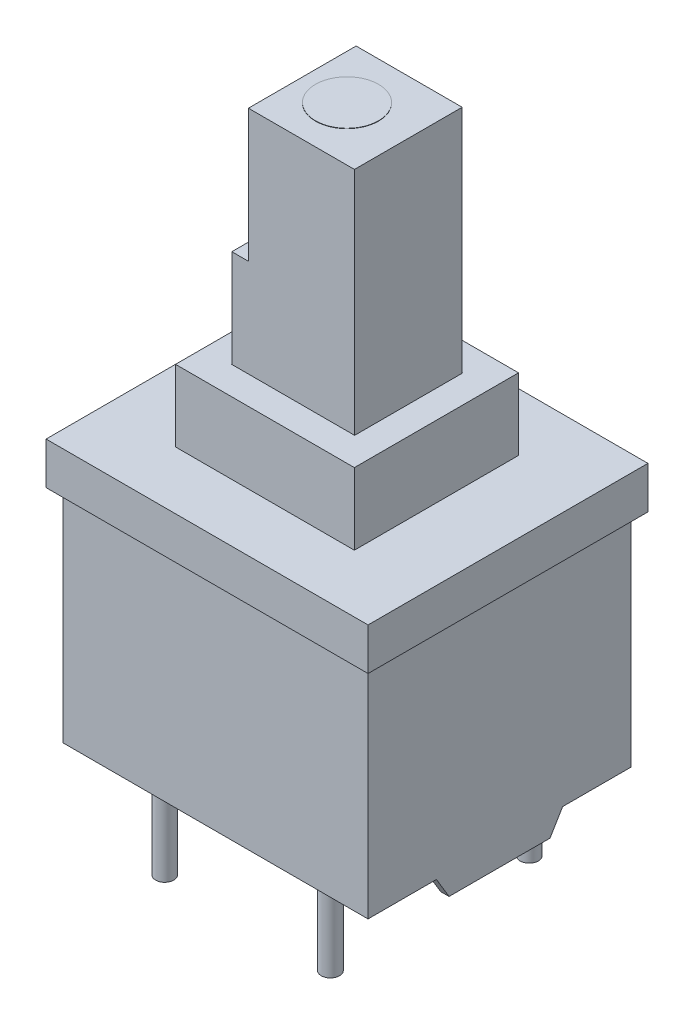
SolidWorks part; units mm, degrees
ref_plane "Front Plane" through (0, 0, 0) normal (0, 0, 1) x (1, 0, 0)
ref_plane "Top Plane" through (0, 0, 0) normal (0, 1, 0) x (1, 0, 0)
ref_plane "Right Plane" through (0, 0, 0) normal (1, 0, 0) x (0, 0, -1)
sketch "Sketch1" plane through (0, 0, 0) normal (0, 1, 0) x (1, 0, 0)
  line L0 (0, 0) -> (0, 69.9245) construction
  line L1 (0, 0) -> (50.231, 0) construction
  line L2 (-4.6038, 3.9688) -> (4.6038, 3.9688)
  line L3 (4.6038, 3.9688) -> (4.6038, -3.9688)
  line L4 (-4.6038, 3.9688) -> (-4.6038, -3.9688)
  line L5 (-4.6038, -3.9688) -> (4.6038, -3.9688)
  point P3 (0, -3.9688)
  point P9 (0, 3.9688)
  point P11 (-4.6038, 0)
  point P12 (4.6038, 0)
  dimension "D1" = 9.2075
  dimension "D2" = 7.9375
extrude "Boss-Extrude1" add sketch "Sketch1" along normal blind 7.9375
sketch "Sketch2" plane through (0, 7.9375, 0) normal (0, 1, 0) x (1, 0, 0)
  line L0 (0, 0) -> (0, 3.9688) construction
  line L1 (0, 0) -> (4.6038, 0) construction
  line L2 (-2.6987, 2.4765) -> (2.6987, 2.4765)
  line L3 (2.6987, 2.4765) -> (2.6987, -2.4765)
  line L4 (4.6038, -3.9688) -> (4.6038, 3.9688)
  line L5 (4.6038, 3.9688) -> (-4.6038, 3.9688)
  line L6 (-4.6038, 3.9688) -> (-4.6038, -3.9688)
  line L7 (-4.6038, -3.9688) -> (4.6038, -3.9688)
  line L8 (4.6038, -3.9688) -> (4.6038, 3.9688)
  line L9 (4.6038, 3.9688) -> (-4.6038, 3.9688)
  line L10 (-4.6038, 3.9688) -> (-4.6038, -3.9688)
  line L11 (-4.6038, -3.9688) -> (4.6038, -3.9688)
  line L12 (-2.6987, 2.4765) -> (-2.6987, -2.4765)
  line L13 (-2.6987, -2.4765) -> (2.6987, -2.4765)
  point P7 (0, -2.4765)
  point P13 (0, 2.4765)
  point P15 (-2.6988, 0)
  point P16 (2.6988, 0)
  dimension "D2" = 5.3975
  dimension "D3" = 4.953
  dimension "D1" = 0
extrude "Boss-Extrude2" add sketch "Sketch2" along normal blind 2.159 contours L12 L13 L3 L2
sketch "Sketch3" plane through (0, 10.0965, 0) normal (0, 1, 0) x (1, 0, 0)
  line L0 (0, 0) -> (0, 2.4765) construction
  line L1 (0, 0) -> (2.6988, 0) construction
  line L2 (-1.86, 1.63) -> (1.86, 1.63)
  line L3 (1.86, 1.63) -> (1.86, -1.63)
  line L4 (-2.6988, 2.4765) -> (-2.6987, -2.4765)
  line L5 (-2.6987, -2.4765) -> (2.6987, -2.4765)
  line L6 (2.6987, -2.4765) -> (2.6988, 2.4765)
  line L7 (2.6988, 2.4765) -> (-2.6988, 2.4765)
  line L8 (-2.6988, 2.4765) -> (-2.6987, -2.4765)
  line L9 (-2.6987, -2.4765) -> (2.6987, -2.4765)
  line L10 (2.6987, -2.4765) -> (2.6988, 2.4765)
  line L11 (2.6988, 2.4765) -> (-2.6988, 2.4765)
  line L12 (-1.86, -1.63) -> (1.86, -1.63)
  line L13 (-1.86, 1.63) -> (-1.86, -1.63)
  point P12 (1.86, 0)
  point P13 (-1.86, 0)
  point P15 (0, -1.63)
  point P16 (0, 1.63)
  dimension "D2" = 3.72
  dimension "D3" = 3.26
  dimension "D1" = 0
extrude "Cut-Extrude1" cut sketch "Sketch3" against normal blind 1.778 contours L2 L13 L12 L3
sketch "Sketch4" plane through (0, 7.9375, 0) normal (0, 1, 0) x (1, 0, 0)
  line L0 (-2.6988, 2.4765) -> (-2.6987, -2.4765) construction
  line L1 (-2.6988, 2.4765) -> (2.6988, 2.4765) construction
  line L2 (2.6988, 2.4765) -> (2.6987, -2.4765) construction
  line L3 (-2.6987, -2.4765) -> (2.6987, -2.4765) construction
  line L12 (-2.6988, 2.4765) -> (-2.6987, -2.4765)
  line L13 (-2.6988, 2.4765) -> (2.6988, 2.4765)
  line L14 (2.6988, 2.4765) -> (2.6987, -2.4765)
  line L15 (-2.6987, -2.4765) -> (2.6987, -2.4765)
  line L16 (-4.8578, -4.2227) -> (4.8578, -4.2227)
  line L17 (4.8578, -4.2227) -> (4.8578, 4.2227)
  line L18 (4.8578, 4.2227) -> (-4.8578, 4.2227)
  line L19 (-4.8578, 4.2227) -> (-4.8578, -4.2227)
  line L20 (-4.8578, -4.2227) -> (4.8578, -4.2227)
  line L21 (4.8578, -4.2227) -> (4.8578, 4.2227)
  line L22 (4.8578, 4.2227) -> (-4.8578, 4.2227)
  line L23 (-4.8578, 4.2227) -> (-4.8578, -4.2227)
  dimension "D1" = 0.254
extrude "Boss-Extrude3" add sketch "Sketch4" against normal blind 1.27
sketch "Sketch5" plane through (4.6038, 0, 0) normal (1, 0, 0) x (0, 0, -1)
  line L0 (0, 0) -> (0, -3.8439) construction
  line L1 (1.905, 0) -> (1.524, -0.635)
  line L2 (1.524, -0.635) -> (-1.524, -0.635)
  line L3 (-1.905, 0) -> (-1.524, -0.635)
  line L4 (3.9688, 6.6675) -> (-3.9688, 6.6675)
  line L5 (-3.9688, 6.6675) -> (-3.9688, 0)
  line L6 (-3.9688, 0) -> (3.9688, 0)
  line L7 (3.9688, 0) -> (3.9688, 6.6675)
  line L8 (3.9688, 6.6675) -> (-3.9688, 6.6675)
  line L9 (-3.9688, 6.6675) -> (-3.9688, 0)
  line L10 (-3.9688, 0) -> (3.9688, 0)
  line L11 (3.9688, 0) -> (3.9688, 6.6675)
  point P11 (0, -0.635)
  line M5 (3.9688, 6.6675) -> (-3.9688, 6.6675)
  line M6 (-3.9688, 6.6675) -> (-3.9688, 0)
  line M7 (-3.9688, 0) -> (3.9688, 0)
  line M8 (3.9688, 0) -> (3.9688, 6.6675)
  dimension "D2" = 3.048
  dimension "D3" = 0.635
  dimension "D4" = 3.81
  dimension "D1" = 0
extrude "Boss-Extrude4" add sketch "Sketch5" against normal blind 0.254 contours L0 L3 L2 M7 | L10 L0 L2 L1 | L10 M8 M5 M6 M7
mirror "Mirror1" about plane through (0, 0, 0) normal (1, 0, 0) of "Boss-Extrude4"
sketch "Sketch7" plane through (0, 8.3185, 0) normal (0, 1, 0) x (1, 0, 0)
  line L0 (0, 3.3431) -> (0, 0) construction
  line L1 (0, 0) -> (4.4103, 0) construction
  line L2 (-1.85, 1.625) -> (1.85, 1.625)
  line L3 (1.85, 1.625) -> (1.85, -1.625)
  line L4 (-1.85, -1.625) -> (1.85, -1.625)
  line L5 (-1.85, 1.625) -> (-1.85, -1.625)
  point P8 (1.85, 0)
  point P10 (0, -1.625)
  point P11 (0, 1.625)
  dimension "D1" = 3.7
  dimension "D2" = 3.25
extrude "Boss-Extrude6" add sketch "Sketch7" along normal blind 8.72
sketch "Sketch8" plane through (0, 17.0385, 0) normal (0, 1, 0) x (1, 0, 0)
  line L0 (0, 3.5495) -> (0, 0) construction
  line L1 (0, 0) -> (3.8936, 0) construction
  line L2 (-1.35, 1.625) -> (-1.35, -1.625)
  line L6 (1.85, -1.625) -> (1.85, 1.625)
  line L7 (1.85, 1.625) -> (-1.85, 1.625)
  line L8 (-1.85, 1.625) -> (-1.85, -1.625)
  line L9 (-1.85, -1.625) -> (1.85, -1.625)
  line L10 (1.85, -1.625) -> (1.85, 1.625)
  line L11 (1.85, 1.625) -> (-1.85, 1.625)
  line L12 (-1.85, 1.625) -> (-1.85, -1.625)
  line L13 (-1.85, -1.625) -> (1.85, -1.625)
  line M6 (1.85, 1.625) -> (-1.85, 1.625)
  line M7 (-1.85, 1.625) -> (-1.85, -1.625)
  line M8 (-1.85, -1.625) -> (1.85, -1.625)
  dimension "D2" = 3.2
  dimension "D1" = 0
extrude "Cut-Extrude2" cut sketch "Sketch8" against normal blind 4 contours L2 M6 M7 M8
sketch "Sketch6" plane through (0, 8.3185, 0) normal (0, 1, 0) x (1, 0, 0)
  line L0 (0, -1.63) -> (0, 1.63) construction
  line L1 (-1.86, 0) -> (1.86, 0) construction
  line L4 (1.86, 1.63) -> (-1.86, 1.63)
  line L5 (-1.86, 1.63) -> (-1.86, -1.63)
  line L6 (-1.86, -1.63) -> (1.86, -1.63)
  line L7 (1.86, -1.63) -> (1.86, 1.63)
  line L8 (1.86, 1.63) -> (-1.86, 1.63)
  line L9 (-1.86, 1.63) -> (-1.86, -1.63)
  line L10 (-1.86, -1.63) -> (1.86, -1.63)
  line L11 (1.86, -1.63) -> (1.86, 1.63)
  circle A0 centre (0, 0) radius 0.9525
  dimension "D2" = 1.905
  dimension "D1" = 0
extrude "Boss-Extrude5" add sketch "Sketch6" along normal offset from surface (8.73 mm away) 0.01 contours A0 up to face at (0.25, 17.0385, 0) offset beyond the face yes
sketch "Sketch9" plane through (0, 0, 0) normal (0, -1, 0) x (1, 0, 0)
  line L0 (0, 6.1244) -> (0, 0) construction
  line L1 (0, 0) -> (7.0971, 0) construction
  circle A0 centre (-2.5, 3) radius 0.275
  circle A1 centre (2.5, 3) radius 0.275
  circle A2 centre (2.5, -3) radius 0.275
  circle A3 centre (-2.5, -3) radius 0.275
  dimension "D3" = 0.55
  dimension "D1" = 5
  dimension "D2" = 6
extrude "Boss-Extrude7" add sketch "Sketch9" along normal blind 2.885
